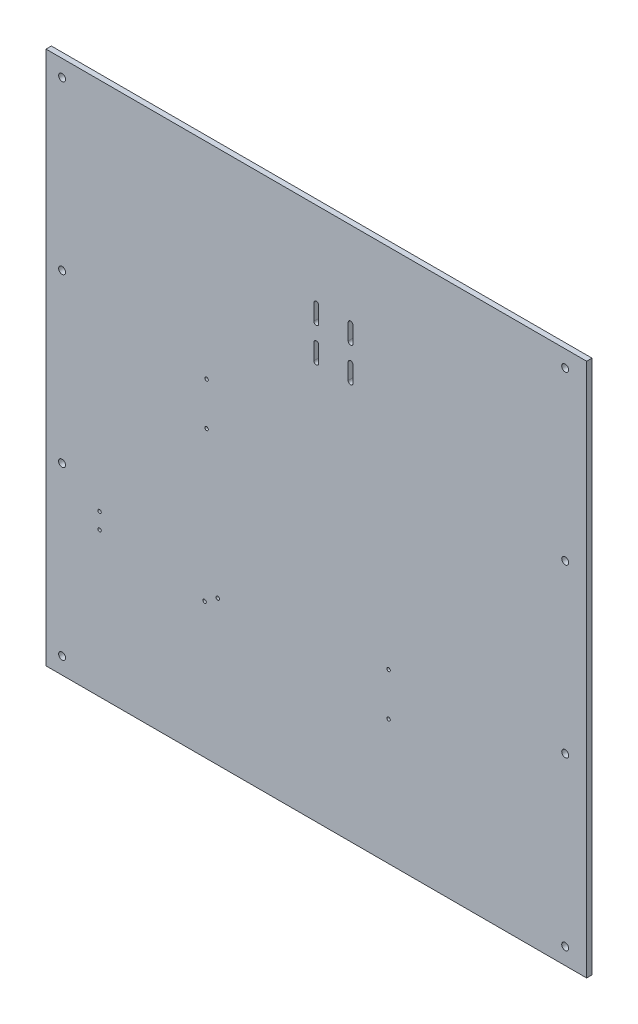
SolidWorks part; units mm, degrees
material "Acrylic (Medium-high impact)"
ref_plane "Front Plane" through (0, 0, 0) normal (0, 0, 1) x (1, 0, 0)
ref_plane "Top Plane" through (0, 0, 0) normal (0, 1, 0) x (1, 0, 0)
ref_plane "Right Plane" through (0, 0, 0) normal (1, 0, 0) x (0, 0, -1)
sketch "Model" plane through (0, 0, 0) normal (0, 0, 1) x (1, 0, 0)
  line L0 (250.25, 404) -> (250.25, 419)
  line L1 (254.75, 419) -> (254.75, 404)
  line L2 (254.75, 387) -> (254.75, 372)
  line L3 (250.25, 372) -> (250.25, 387)
  line L4 (286.75, 387) -> (286.75, 372)
  line L5 (282.25, 372) -> (282.25, 387)
  line L6 (286.75, 419) -> (286.75, 404)
  line L7 (282.25, 404) -> (282.25, 419)
  line L8 (505, 0) -> (0, 0)
  line L9 (0, 0) -> (0, 499)
  line L10 (0, 499) -> (505, 499)
  line L11 (505, 499) -> (505, 0)
  circle A0 centre (160.4092, 134.9884) radius 1.6
  circle A1 centre (50, 135) radius 1.6
  circle A2 centre (148.1219, 126.3847) radius 1.6
  circle A3 centre (50, 150) radius 1.6
  circle A4 centre (150, 267) radius 1.6
  circle A5 centre (150, 307) radius 1.6
  circle A6 centre (320, 117) radius 1.6
  circle A7 centre (15, 15.5) radius 3.25
  circle A8 centre (485, 15.5) radius 3.25
  circle A9 centre (15, 171.5) radius 3.25
  circle A10 centre (485, 171.5) radius 3.25
  circle A11 centre (15, 327.5) radius 3.25
  circle A12 centre (485, 327.5) radius 3.25
  circle A13 centre (15, 483.5) radius 3.25
  circle A14 centre (485, 483.5) radius 3.25
  circle A15 centre (320, 157) radius 1.6
  arc A16 (250.25, 404) -> (254.75, 404) centre (252.5, 404) ccw
  arc A17 (254.75, 419) -> (250.25, 419) centre (252.5, 419) ccw
  arc A18 (254.75, 387) -> (250.25, 387) centre (252.5, 387) ccw
  arc A19 (250.25, 372) -> (254.75, 372) centre (252.5, 372) ccw
  arc A20 (286.75, 387) -> (282.25, 387) centre (284.5, 387) ccw
  arc A21 (282.25, 372) -> (286.75, 372) centre (284.5, 372) ccw
  arc A22 (286.75, 419) -> (282.25, 419) centre (284.5, 419) ccw
  arc A23 (282.25, 404) -> (286.75, 404) centre (284.5, 404) ccw
  dimension "D1" = 3.2
  dimension "D2" = 6.5
  dimension "D3" = 2.25
  dimension "D4" = 15
  dimension "D5" = 50
  dimension "D6" = 148.1219
  dimension "D7" = 150
  dimension "D8" = 160.4092
  dimension "D9" = 252.5
  dimension "D10" = 284.5
  dimension "D11" = 320
  dimension "D12" = 485
  dimension "D13" = 505
  dimension "D14" = 15.5
  dimension "D15" = 117
  dimension "D16" = 126.3847
  dimension "D17" = 134.9884
  dimension "D18" = 135
  dimension "D19" = 150
  dimension "D20" = 157
  dimension "D21" = 171.5
  dimension "D22" = 267
  dimension "D23" = 307
  dimension "D24" = 327.5
  dimension "D25" = 372
  dimension "D26" = 387
  dimension "D27" = 404
  dimension "D29" = 483.5
  dimension "D30" = 499
extrude "Boss-Extrude1" add sketch "Model" along normal blind 5
